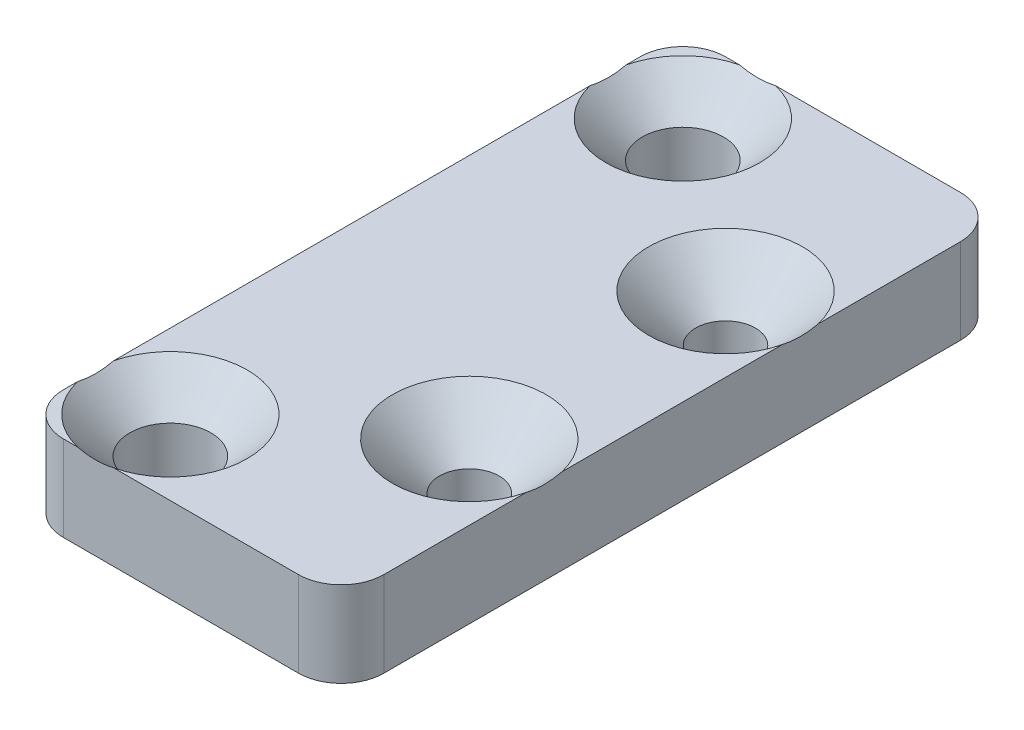
SolidWorks part; units mm, degrees
ref_plane "Front Plane" through (0, 0, 0) normal (0, 0, 1) x (1, 0, 0)
ref_plane "Top Plane" through (0, 0, 0) normal (0, 1, 0) x (1, 0, 0)
ref_plane "Right Plane" through (0, 0, 0) normal (1, 0, 0) x (0, 0, -1)
sketch "Sketch1" plane through (0, 0, 0) normal (0, 1, 0) x (1, 0, 0)
  line L5 (-2.75, 7.75) -> (2.75, 7.75)
  line L6 (-3.75, 6.75) -> (-3.75, -6.75)
  line L7 (-2.75, -7.75) -> (2.75, -7.75)
  line L8 (3.75, 6.75) -> (3.75, -6.75)
  line L9 (-3.75, 7.75) -> (3.75, -7.75) construction
  line L10 (-3.75, -7.75) -> (3.75, 7.75) construction
  line L11 (-4, 8) -> (4, 8) construction
  line L12 (-4, 8) -> (-4, -8) construction
  line L13 (-4, -8) -> (4, -8) construction
  line L14 (4, 8) -> (4, -8) construction
  line L15 (-4, 8) -> (4, -8) construction
  line L16 (-4, -8) -> (4, 8) construction
  arc A0 (-3.75, -6.75) -> (-2.75, -7.75) centre (-2.75, -6.75) ccw
  arc A1 (2.75, -7.75) -> (3.75, -6.75) centre (2.75, -6.75) ccw
  arc A2 (2.75, 7.75) -> (3.75, 6.75) centre (2.75, 6.75) cw
  arc A3 (-2.75, 7.75) -> (-3.75, 6.75) centre (-2.75, 6.75) ccw
  circle A4 centre (-2, 6) radius 0.95
  circle A5 centre (-2, -6) radius 0.95
  circle A6 centre (2, 3) radius 0.7
  circle A7 centre (2, -3) radius 0.7
  point P0 (0, 0)
  point P19 (0, 0)
  dimension "D3" = 1
  dimension "D6" = 12
  dimension "D8" = 1.9
  dimension "D9" = 1.4
  dimension "D13" = 2
  dimension "D1" = 15.5
  dimension "D2" = 7.5
  dimension "D4" = 8
  dimension "D5" = 16
  dimension "D7" = 6
  dimension "D10" = 6
  dimension "D11" = 3
  dimension "D12" = 2
  dimension "D14" = 4
  dimension "D15" = 4
extrude "Boss-Extrude1" add sketch "Sketch1" along normal blind 2
hole_wizard "CSK for M2 Flat Head Machine Screw1" positions "3DSketch1" profile "Sketch2" countersink size "M2" standard "ANSI Metric"
sketch3d "3DSketch1"
  line L0 (-2, 2, 6) -> (-2, 0, 6) construction
  line L1 (-2, 2, -6) -> (-2, 0, -6) construction
  line L2 (2, 2, 3) -> (2, 0, 3) construction
  line L3 (2, 2, -3) -> (2, 0, -3) construction
  point P0 (-2, 2, 6)
  point P4 (-2, 2, -6)
  point P13 (-4.7379, 0, 2.5993)
  point P17 (2, 2, 3)
  point P21 (2, 2, -3)
sketch "Sketch2" plane through (-2, 2, 6) normal (1, 0, 0) x (0, 0, 1)
  line L0 (0, 0) -> (0, 2)
  line L1 (0, 2) -> (0.7, 2)
  line L2 (0.7, 2) -> (0.7, 1.1)
  line L3 (0.7, 1.1) -> (1.8, 0)
  line L5 (1.8, 0) -> (0, 0)
  line L6 (-0.7, 1.1) -> (-1.8, 0) construction
  line L11 (0, -6.35) -> (0, 107.95) construction
  dimension "Thru Hole Dia." = 1.4
  dimension "Thru Hole Depth" = 2
  dimension "Near C'Sink Dia." = 3.6
  dimension "Near C'Sink Angle" = 90
